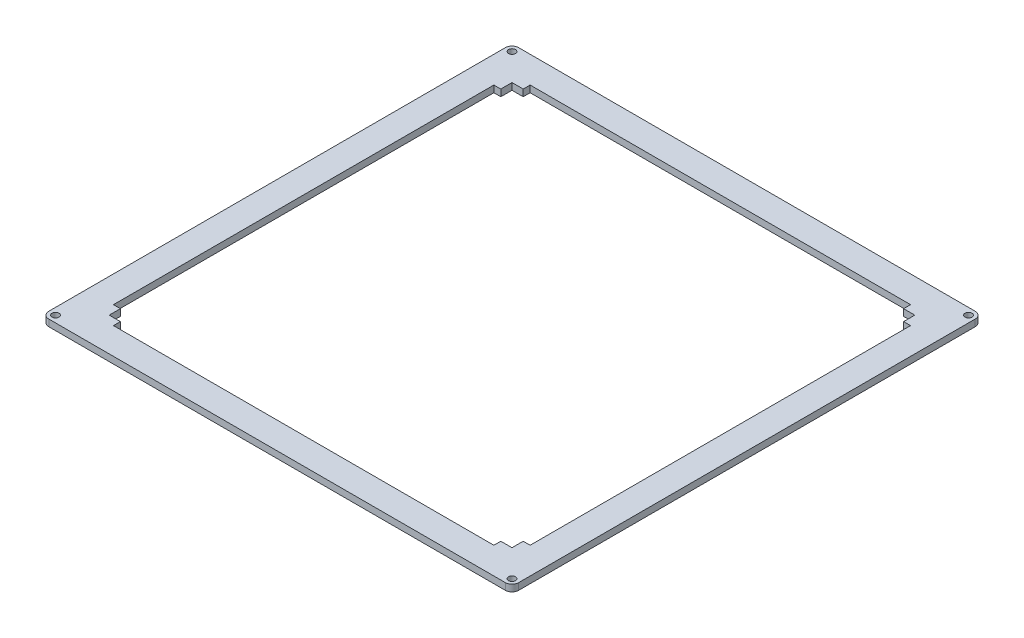
SolidWorks part; units mm, degrees
ref_plane "前视基准面" through (0, 0, 0) normal (0, 0, 1) x (1, 0, 0)
ref_plane "上视基准面" through (0, 0, 0) normal (0, 1, 0) x (1, 0, 0)
ref_plane "右视基准面" through (0, 0, 0) normal (1, 0, 0) x (0, 0, -1)
sketch "草图3" plane through (0, 0, 0) normal (0, 1, 0) x (1, 0, 0)
  line L0 (0, 3) -> (0, 15)
  line L1 (3, 0) -> (207, 0)
  line L2 (0, 3) -> (0, 207)
  line L3 (3, 210) -> (207, 210)
  line L4 (210, 3) -> (210, 207)
  line L5 (0, 15) -> (15, 15) construction
  line L6 (15, 15) -> (15, 0) construction
  line L7 (207, 210) -> (195, 210)
  line L8 (195, 210) -> (195, 195) construction
  line L9 (195, 195) -> (198.1, 195) construction
  line L11 (195, 195) -> (15, 195)
  line L12 (195, 195) -> (195, 15)
  line L13 (195, 15) -> (15, 15)
  line L14 (15, 195) -> (15, 15)
  line L15 (0, 195) -> (15, 195) construction
  line L16 (0, 195) -> (0, 207)
  line L17 (3, 210) -> (15, 210)
  line L18 (15, 195) -> (15, 210) construction
  line L19 (195, 15) -> (198.1, 15) construction
  line L20 (195, 15) -> (195, 0) construction
  line L21 (195, 0) -> (207, 0)
  line L22 (210, 15) -> (210, 3)
  line L23 (11.9, 175) -> (11.9, 35)
  line L26 (35, 11.9) -> (175, 11.9)
  line L27 (175, 11.9) -> (185, 11.9) construction
  line L29 (198.1, 35) -> (198.1, 175)
  line L30 (195, 15) -> (190, 15)
  line L31 (15, 195) -> (35, 195)
  line L32 (175, 198.1) -> (35, 198.1)
  line L33 (195, 195) -> (195, 175)
  line L35 (3, 0) -> (3, 3) construction
  line L37 (3, 210) -> (3, 207) construction
  line L39 (207, 210) -> (207, 207) construction
  line L41 (207, 0) -> (207, 3) construction
  line L42 (15, 195) -> (18, 195)
  line L43 (18, 195) -> (18, 192) construction
  line L44 (195, 195) -> (192, 195)
  line L45 (192, 195) -> (192, 192) construction
  line L46 (195, 15) -> (192, 15)
  line L47 (192, 15) -> (192, 18) construction
  line L48 (15, 15) -> (18, 15)
  line L49 (18, 15) -> (18, 18) construction
  line L50 (195, 195) -> (175, 195)
  line L51 (35, 198.1) -> (20, 198.1)
  line L52 (3, 3) -> (0, 3) construction
  line L53 (175, 198.1) -> (190, 198.1)
  line L54 (195, 15) -> (195, 35)
  line L55 (195, 195) -> (195, 190)
  line L56 (195, 15) -> (175, 15)
  line L57 (195, 15) -> (195, 20)
  line L58 (15, 15) -> (15, 35)
  line L59 (15, 15) -> (20, 15)
  line L60 (15, 195) -> (15, 175)
  line L61 (15, 15) -> (15, 20)
  line L69 (25, 11.9) -> (35, 11.9) construction
  line L70 (11.9, 35) -> (11.9, 25) construction
  line L71 (198.1, 35) -> (198.1, 15) construction
  line L75 (201.2, 15) -> (210, 15) construction
  line L77 (201.2, 15) -> (198.1, 15) construction
  line L81 (198.1, 175) -> (198.1, 195) construction
  line L86 (175, 198.1) -> (195, 198.1) construction
  line L91 (35, 198.1) -> (15, 198.1) construction
  line L96 (11.9, 175) -> (11.9, 195) construction
  line L101 (15, 195) -> (15, 190)
  line L102 (15, 190) -> (11.9, 190)
  line L103 (11.9, 190) -> (11.9, 175)
  line L104 (15, 20) -> (11.9, 20)
  line L105 (11.9, 20) -> (11.9, 35)
  line L106 (20, 15) -> (20, 11.9)
  line L107 (20, 11.9) -> (35, 11.9)
  line L108 (190, 15) -> (190, 11.9)
  line L109 (190, 11.9) -> (175, 11.9)
  line L110 (195, 20) -> (198.1, 20)
  line L111 (198.1, 20) -> (198.1, 35)
  line L112 (195, 190) -> (198.1, 190)
  line L113 (198.1, 190) -> (198.1, 175)
  line L114 (190, 198.1) -> (190, 195)
  line L115 (20, 198.1) -> (20, 195)
  line L116 (3, 207) -> (0, 207) construction
  line L117 (207, 207) -> (210, 207) construction
  line L118 (207, 3) -> (210, 3) construction
  circle A0 centre (3, 3) radius 1.55
  circle A1 centre (3, 207) radius 1.55
  circle A2 centre (207, 207) radius 1.55
  circle A3 centre (207, 3) radius 1.55
  circle A4 centre (18, 192) radius 1.55
  circle A5 centre (192, 192) radius 1.55
  circle A6 centre (192, 18) radius 1.55
  circle A7 centre (18, 18) radius 1.55
  arc A8 (0, 207) -> (3, 210) centre (3, 207) cw
  arc A9 (207, 210) -> (210, 207) centre (207, 207) cw
  arc A10 (210, 3) -> (207, 0) centre (207, 3) cw
  arc A11 (3, 0) -> (0, 3) centre (3, 3) cw
extrude "凸台-拉伸1" add sketch "草图3" along normal blind 3 contours A11 L1 A10 L4 A9 L3 A8 L2 L0 A3 A2 A1 A0 L115 L51 L32 L53 L114 L11 L12 L112 L113 L29 L111 L110 L54 L13 L30 L108 L109 L26 L107 L106 L58 L104 L105 L23 L103
